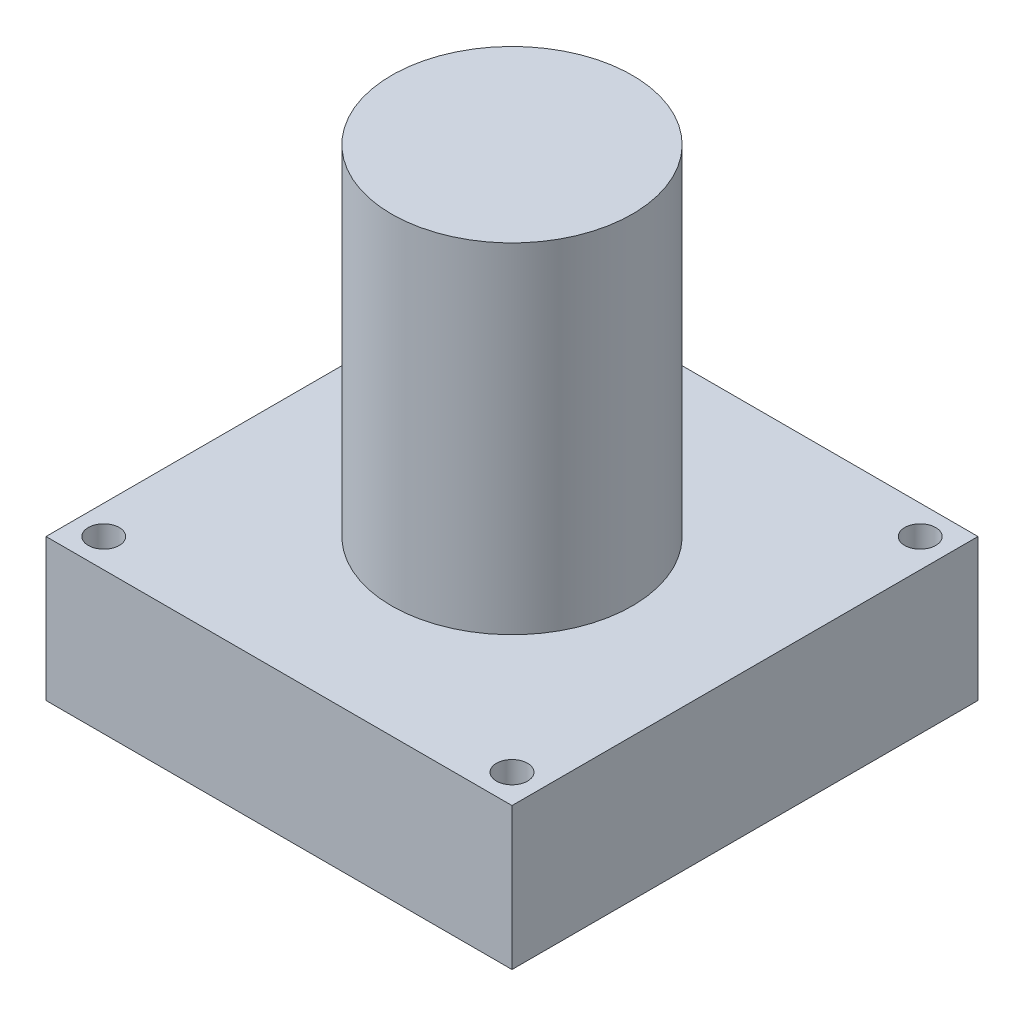
SolidWorks part; units mm, degrees
ref_plane "Front Plane" through (0, 0, 0) normal (0, 0, 1) x (1, 0, 0)
ref_plane "Top Plane" through (0, 0, 0) normal (0, 1, 0) x (1, 0, 0)
ref_plane "Right Plane" through (0, 0, 0) normal (1, 0, 0) x (0, 0, -1)
sketch "Sketch1" plane through (0, 0, 0) normal (0, 1, 0) x (1, 0, 0)
  line L1 (0, 0) -> (30, 0)
  line L2 (0, 0) -> (0, 30)
  line L3 (0, 30) -> (30, 30)
  line L4 (30, 0) -> (30, 30)
  circle A0 centre (1.86, 1.86) radius 1
  circle A1 centre (1.86, 28.14) radius 1
  circle A2 centre (28.14, 28.14) radius 1
  circle A3 centre (28.14, 1.86) radius 1
  dimension "D5" = 2
  dimension "D1" = 30
  dimension "D2" = 30
  dimension "D3" = 1.86
  dimension "D4" = 1.86
  dimension "D6" = 1.86
  dimension "D7" = 1.86
extrude "Boss-Extrude1" add sketch "Sketch1" along normal blind 9.144 contours L1 L4 L3 L2 A3 A2 A1 A0
sketch "Sketch2" plane through (0, 9.144, 0) normal (0, 1, 0) x (1, 0, 0)
  line L0 (0, 0) -> (30, 0) construction
  line L1 (30, 0) -> (30, 30) construction
  circle A0 centre (15, 15) radius 7.747
  point P5 (15, 0)
  point P10 (30, 15)
  dimension "D1" = 15.494
extrude "Boss-Extrude2" add sketch "Sketch2" along normal blind 21.844
sketch "Sketch3" plane through (0, 0, 0) normal (0, -1, 0) x (1, 0, 0)
  line L0 (0, -30) -> (30, -30) construction
  line L1 (8.3325, -24.666) -> (21.6675, -24.666)
  line L2 (8.3325, -24.666) -> (8.3325, -27.714)
  line L3 (8.3325, -27.714) -> (21.6675, -27.714)
  line L4 (21.6675, -24.666) -> (21.6675, -27.714)
  point P6 (15, -30)
  point P7 (15, -27.714)
  dimension "D1" = 13.335
  dimension "D2" = 3.048
  dimension "D3" = 2.286
extrude "Boss-Extrude3" add sketch "Sketch3" along normal blind 6.35
